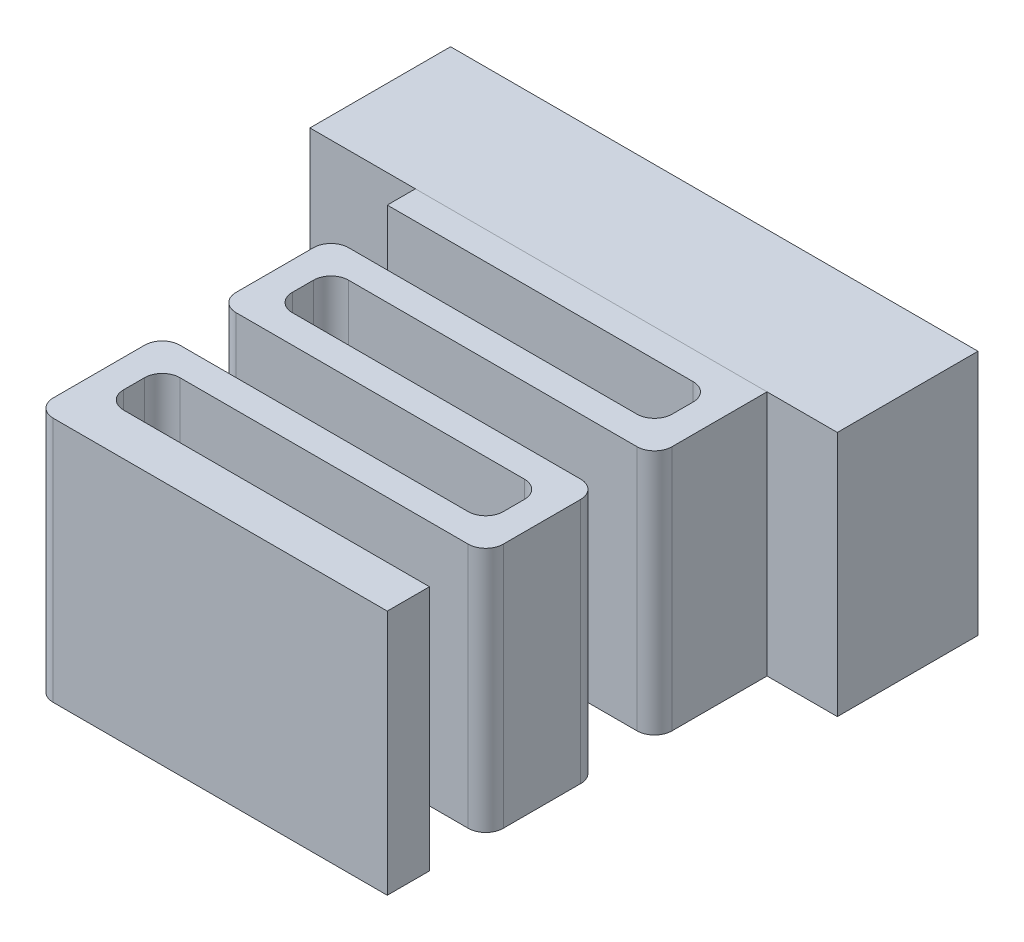
SolidWorks part; units mm, degrees
ref_plane "Front Plane" through (0, 0, 0) normal (0, 0, 1) x (1, 0, 0)
ref_plane "Top Plane" through (0, 0, 0) normal (0, 1, 0) x (1, 0, 0)
ref_plane "Right Plane" through (0, 0, 0) normal (1, 0, 0) x (0, 0, -1)
sketch "스케치1" plane through (0, 0, 0) normal (0, 0, 1) x (1, 0, 0)
  line L0 (0, 0) -> (50000, 0) construction
  line L1 (0, 0) -> (0, 50000) construction
  line L3 (-48, 3.5) -> (-33, 3.5)
  line L4 (-48, 3.5) -> (-48, -3.5)
  line L5 (-48, -3.5) -> (-33, -3.5)
  line L6 (-33, 3.5) -> (-33, -3.5)
  dimension "D1" = 15
  dimension "D2" = 7
  dimension "D3" = 3.5
  dimension "D4" = 48
extrude "보스-돌출1" add sketch "스케치1" along normal blind 4
sketch "스케치2" plane through (0, 3.5, 0) normal (0, 1, 0) x (1, 0, 0)
  line L0 (0, 0) -> (0, -50000) construction
  line L1 (-40, 7.7588) -> (-40, -49992.2412) construction
  line L2 (40, 11.8931) -> (40, -49988.1069) construction
  line L3 (-45.6485, -4.8) -> (49954.3515, -4.8) construction
  line L4 (-46.2771, -6.4) -> (49953.7229, -6.4) construction
  line L5 (-47.4446, -7.2) -> (49952.5554, -7.2) construction
  line L6 (-33, -4) -> (-48, -4) construction
  line L7 (-45, -7) -> (-45, -50007) construction
  line L8 (-35, -7) -> (-35, -50007) construction
  line L9 (-48.5931, -8.8) -> (49951.4069, -8.8) construction
  line L10 (-49.1433, -9.6) -> (49950.8567, -9.6) construction
  line L11 (-44.2, 2.343) -> (-44.2, -49997.657) construction
  line L12 (-35.8, 2.2207) -> (-35.8, -49997.7793) construction
  line L13 (-35, -4) -> (-45, -4)
  line L14 (-45, -4) -> (-45, -4.8)
  line L15 (-35.8, -6.4) -> (-35.8, -4.8)
  line L16 (-35.8, -4.8) -> (-45, -4.8)
  line L17 (-35.8, -6.4) -> (-45, -6.4)
  line L18 (-45, -6.4) -> (-45, -9.6)
  line L19 (-45, -9.6) -> (-35.8, -9.6)
  line L20 (-35, -9.6) -> (-35, -8.8)
  line L21 (-35, -8.8) -> (-44.2, -8.8)
  line L22 (-44.2, -8.8) -> (-44.2, -7.2)
  line L23 (-44.2, -7.2) -> (-35, -7.2)
  line L24 (-35, -7.2) -> (-35, -4)
  line L25 (-48.6472, -11.2) -> (49951.3528, -11.2) construction
  line L26 (-49.2921, -12) -> (49950.7079, -12) construction
  line L27 (-35.8, -9.6) -> (-35.8, -11.2)
  line L28 (-35.8, -11.2) -> (-45, -11.2)
  line L29 (-45, -11.2) -> (-45, -12)
  line L30 (-45, -12) -> (-45, -14.8)
  line L31 (-35, -12) -> (-35, -9.6)
  line L32 (-46.6391, -13.6) -> (-35, -13.6) construction
  line L33 (-35, -13.6) -> (-35, -14.8) construction
  line L34 (-35, -14.8) -> (-45, -14.8) construction
  line L35 (-45, -14.8) -> (-35, -14.8)
  line L36 (-35, -14.8) -> (-35, -13.6)
  line L37 (-35, -13.6) -> (-44.2, -13.6)
  line L38 (-44.2, -13.6) -> (-44.2, -12)
  line L39 (-44.2, -12) -> (-35, -12)
  dimension "D8" = 1.6
  dimension "D1" = 40
  dimension "D2" = 40
  dimension "D3" = 0.8
  dimension "D4" = 5
  dimension "D5" = 5
  dimension "D6" = 1.6
  dimension "D7" = 0.8
  dimension "D9" = 0.8
  dimension "D10" = 0.8
  dimension "D11" = 0.8
  dimension "D12" = 1.6
  dimension "D13" = 0.8
  dimension "D14" = 1.6
  dimension "D15" = 1.2
extrude "보스-돌출2" add sketch "스케치2" against normal blind 7 separate body
fillet "필렛1" radius 0.5 15 edges at (-35, 0, 7.2) (-44.2, 0, 7.2) (-44.2, 0, 8.8) (-35, 0, 8.8) (-35, 0, 12) (-44.2, 0, 12) (-44.2, 0, 13.6) (-45, 0, 14.8) (-45, 0, 11.2) (-35.8, 0, 11.2) (-35.8, 0, 9.6) (-45, 0, 9.6) (-45, 0, 6.4) (-35.8, 0, 6.4) (-35.8, 0, 4.8)
